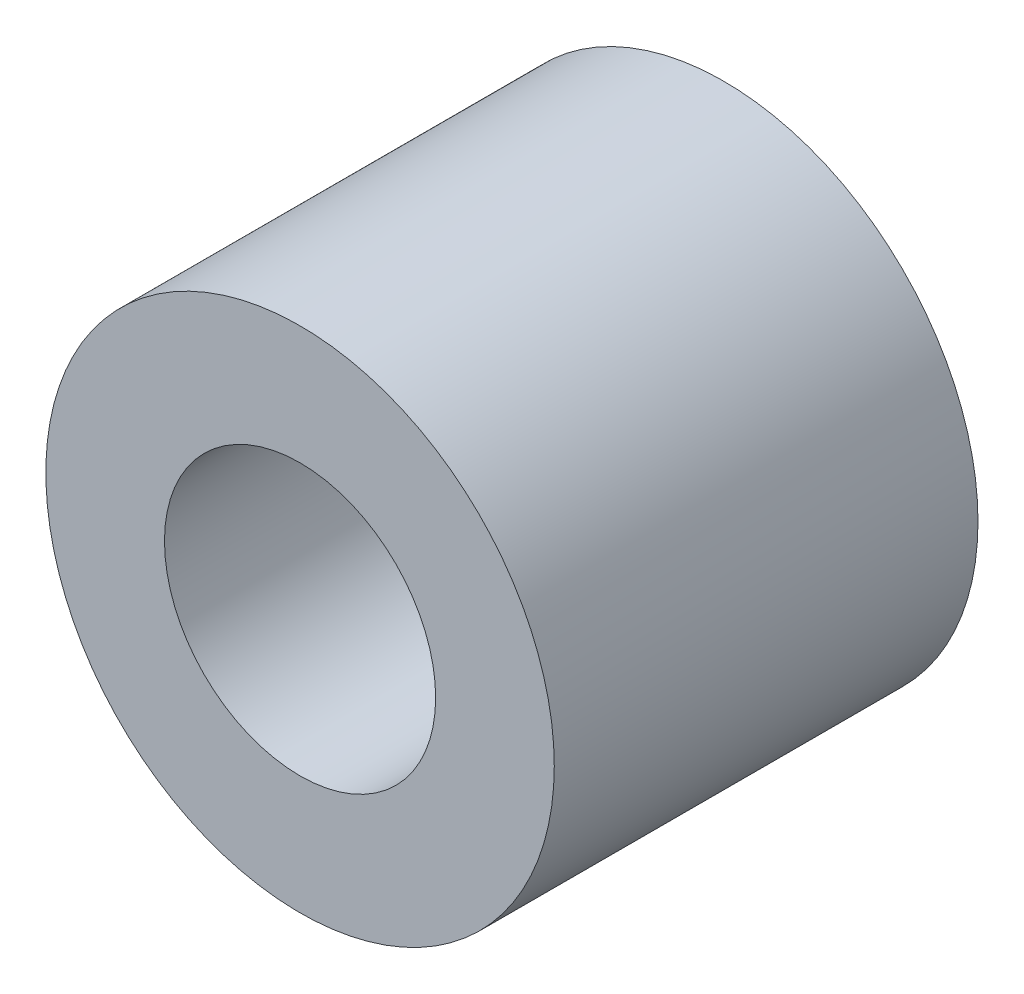
SolidWorks part; units mm, degrees
ref_plane "Front Plane" through (0, 0, 0) normal (0, 0, 1) x (1, 0, 0)
ref_plane "Top Plane" through (0, 0, 0) normal (0, 1, 0) x (1, 0, 0)
ref_plane "Right Plane" through (0, 0, 0) normal (1, 0, 0) x (0, 0, -1)
sketch "Sketch1" plane through (0, 0, 0) normal (0, 0, 1) x (1, 0, 0)
  circle A0 centre (0, 0) radius 1.6
  circle A1 centre (0, 0) radius 3
extrude "Boss-Extrude1" add sketch "Sketch1" along normal blind 5
